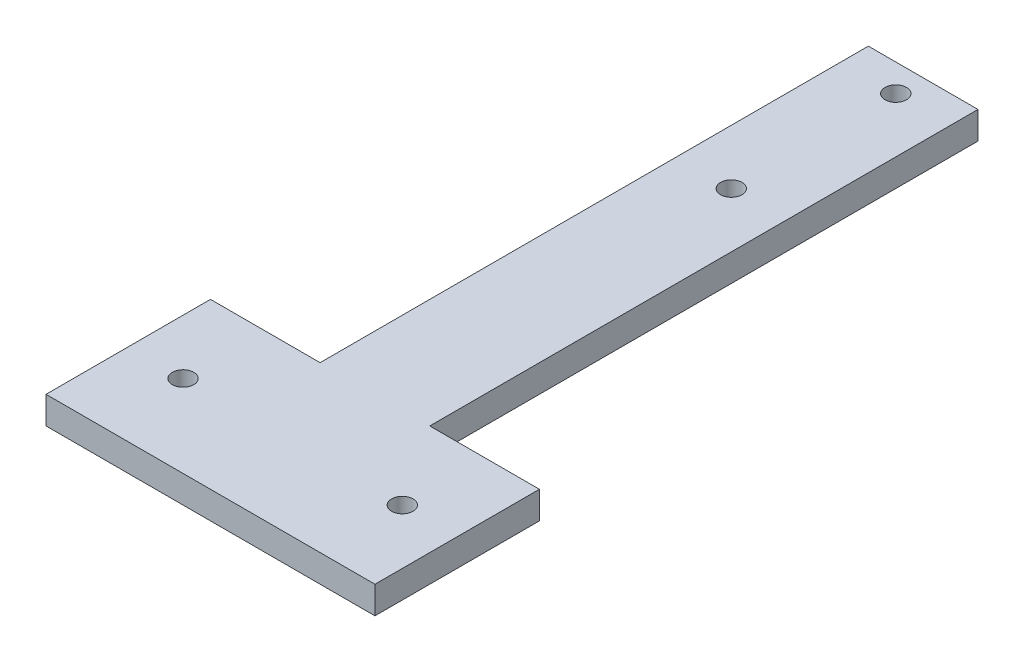
SolidWorks part; units mm, degrees
material "Plain Carbon Steel"
ref_plane "Front Plane" through (0, 0, 0) normal (0, 0, 1) x (1, 0, 0)
ref_plane "Top Plane" through (0, 0, 0) normal (0, 1, 0) x (1, 0, 0)
ref_plane "Right Plane" through (0, 0, 0) normal (1, 0, 0) x (0, 0, -1)
sketch "Sketch2" plane through (0, 0, 0) normal (0, 1, 0) x (1, 0, 0)
  line L0 (-12.7, 165.1) -> (-12.7, 38.1)
  line L1 (-12.7, 38.1) -> (-38.1, 38.1)
  line L2 (-38.1, 38.1) -> (-38.1, 0)
  line L3 (-38.1, 0) -> (38.1, 0)
  line L4 (38.1, 0) -> (38.1, 38.1)
  line L5 (38.1, 38.1) -> (12.7, 38.1)
  line L6 (12.7, 38.1) -> (12.7, 165.1)
  line L7 (12.7, 165.1) -> (-12.7, 165.1)
  line L8 (0, 165.1) -> (0, 0) construction
  line L9 (-38.1, 19.05) -> (38.1, 19.05) construction
  circle A0 centre (-25.4, 19.05) radius 2.4892
  circle A1 centre (25.4, 19.05) radius 2.4892
  circle A2 centre (0, 158.75) radius 2.4892
  circle A3 centre (0, 120.65) radius 2.4892
  point P3 (0, 0)
  dimension "D5" = 4.9784
  dimension "D6" = 12.7
  dimension "D7" = 12.7
  dimension "D8" = 6.35
  dimension "D9" = 38.1
  dimension "D1" = 38.1
  dimension "D2" = 76.2
  dimension "D3" = 25.4
  dimension "D4" = 127
extrude "Boss-Extrude1" add sketch "Sketch2" along normal blind 6.35
equation "\"Thick\"= \"in\""
